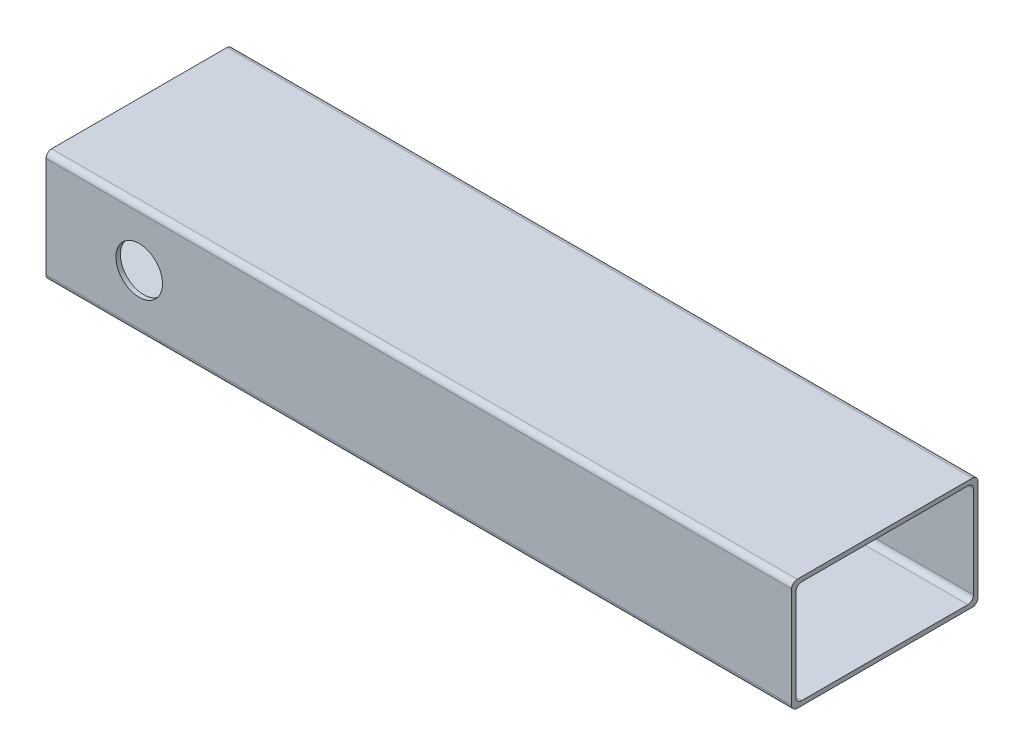
SolidWorks part; units mm, degrees
ref_plane "Front Plane" through (0, 0, 0) normal (0, 0, 1) x (1, 0, 0)
ref_plane "Top Plane" through (0, 0, 0) normal (0, 1, 0) x (1, 0, 0)
ref_plane "Right Plane" through (0, 0, 0) normal (1, 0, 0) x (0, 0, -1)
sketch "Sketch1" plane through (0, 0, 0) normal (0, 1, 0) x (1, 0, 0)
  line L1 (-287.7483, 63.9441) -> (220.2517, 63.9441)
  line L2 (-287.7483, 63.9441) -> (-287.7483, -63.0559)
  line L3 (-287.7483, -63.0559) -> (220.2517, -63.0559)
  line L4 (220.2517, 63.9441) -> (220.2517, -63.0559)
  dimension "D1" = 127
  dimension "D2" = 508
extrude "Boss-Extrude1" add sketch "Sketch1" along normal blind 76.2
sketch "Sketch5" plane through (-287.7483, 0, 0) normal (-1, 0, 0) x (0, 0, 1)
  line L8 (-60.8961, 3.048) -> (60.0079, 3.048)
  line L9 (60.0079, 3.048) -> (60.0079, 73.152)
  line L10 (60.0079, 73.152) -> (-60.8961, 73.152)
  line L11 (-60.8961, 73.152) -> (-60.8961, 3.048)
  line L12 (-60.8961, 3.048) -> (60.0079, 3.048)
  line L13 (60.0079, 3.048) -> (60.0079, 73.152)
  line L14 (60.0079, 73.152) -> (-60.8961, 73.152)
  line L15 (-60.8961, 73.152) -> (-60.8961, 3.048)
  dimension "D1" = 3.048
extrude "Cut-Extrude1" cut sketch "Sketch5" against normal through all
fillet "Fillet1" radius 3.81 8 edges at (-33.7483, 73.152, -60.8961) (-33.7483, 3.048, -60.8961) (-33.7483, 3.048, 60.0079) (-33.7483, 73.152, 60.0079) (-33.7483, 76.2, -63.9441) (-33.7483, 0, -63.9441) (-33.7483, 0, 63.0559) (-33.7483, 76.2, 63.0559)
sketch "Sketch9" plane through (0, 0, 63.0559) normal (0, 0, 1) x (1, 0, 0)
  line L0 (-224.2483, 76.2) -> (-224.2483, 0) construction
  line L1 (-287.7483, 76.2) -> (220.2517, 76.2) construction
  line L2 (-287.7483, 0) -> (220.2517, 0) construction
  line L3 (-224.2483, 38.1) -> (-287.7483, 38.1) construction
  line L4 (-287.7483, 72.39) -> (-287.7483, 3.81) construction
  circle A0 centre (-224.2483, 38.1) radius 15.875
  dimension "D2" = 31.75
  dimension "D1" = 63.5
extrude "Cut-Extrude5" cut sketch "Sketch9" against normal through all
sketch "Sketch10" plane through (0, 0, 0) normal (0, -1, 0) x (1, 0, 0)
  line L0 (220.2517, -0.4441) -> (-287.7483, -0.4441) construction
  line L1 (220.2517, 59.2459) -> (220.2517, -60.1341) construction
  line L2 (-287.7483, -60.1341) -> (-287.7483, 59.2459) construction
